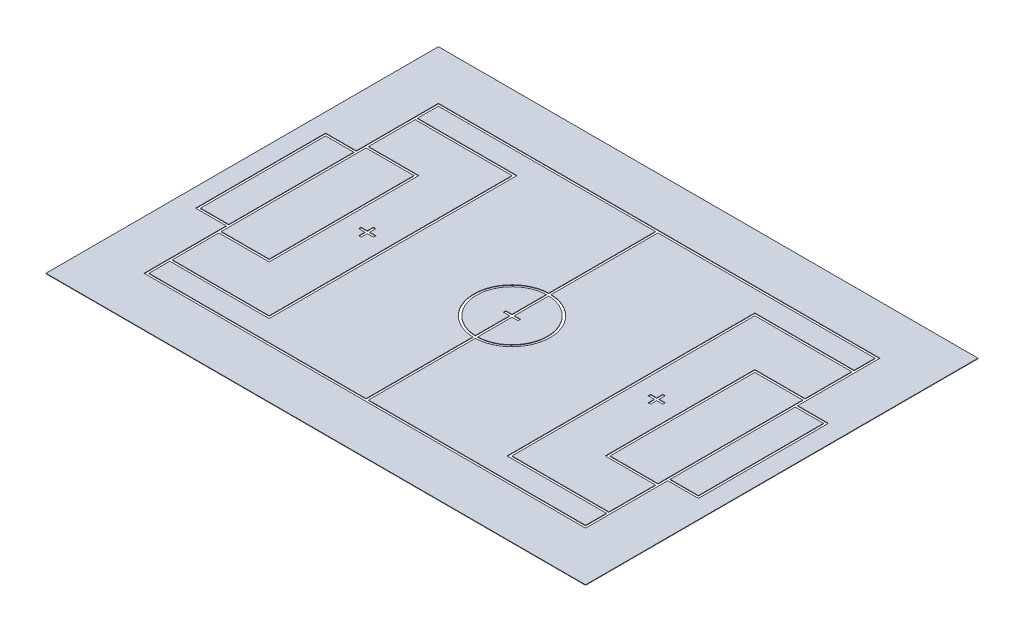
SolidWorks part; units mm, degrees
ref_plane "Front Plane" through (0, 0, 0) normal (0, 0, 1) x (1, 0, 0)
ref_plane "Top Plane" through (0, 0, 0) normal (0, 1, 0) x (1, 0, 0)
ref_plane "Right Plane" through (0, 0, 0) normal (1, 0, 0) x (0, 0, -1)
sketch "Sketch1" plane through (0, 0, 0) normal (0, 1, 0) x (1, 0, 0)
  line L0 (-4450, 2950) -> (-4450, 2525)
  line L1 (-5500, 4000) -> (5500, 4000)
  line L2 (-5500, 4000) -> (-5500, -4000)
  line L3 (-5500, -4000) -> (5500, -4000)
  line L4 (5500, 4000) -> (5500, -4000)
  line L5 (-4500, 3000) -> (4500, 3000)
  line L6 (-4500, 3000) -> (-4500, 1325)
  line L7 (-4500, -3000) -> (4500, -3000)
  line L8 (4500, 3000) -> (4500, 1325)
  line L9 (-4450, -2950) -> (-25, -2950)
  line L10 (4450, 2950) -> (4450, 2525)
  line L11 (-4450, 2950) -> (-25, 2950)
  line L12 (25, -2950) -> (4450, -2950)
  line L13 (-25, 2950) -> (-25, 773.6822)
  line L14 (25, 2950) -> (25, 773.6822)
  line L15 (-4450, -2950) -> (4450, -2950) construction
  line L16 (-25, 723.5912) -> (-25, 25)
  line L17 (25, 723.5912) -> (25, 25)
  line L18 (25, 2950) -> (4450, 2950)
  line L19 (-4450, 2950) -> (4450, 2950) construction
  line L20 (-25, -773.6822) -> (-25, -2950)
  line L21 (25, -773.6822) -> (25, -2950)
  line L22 (-150, 0) -> (150, 0) construction
  line L27 (-150, -25) -> (-25, -25)
  line L28 (-150, 25) -> (-25, 25)
  line L29 (-150, -25) -> (-150, 25)
  line L30 (150, -25) -> (150, 25)
  line L31 (25, 25) -> (150, 25)
  line L32 (-150, 25) -> (150, 25) construction
  line L33 (25, -25) -> (150, -25)
  line L34 (-150, -25) -> (150, -25) construction
  line L35 (-25, -25) -> (-25, -723.5912)
  line L36 (25, -25) -> (25, -723.5912)
  line L37 (-4450, 1500) -> (-3450, 1500) construction
  line L38 (-3450, 1500) -> (-3450, -1500) construction
  line L39 (-3450, -1500) -> (-4450, -1500) construction
  line L40 (-4450, 2500) -> (-2450, 2500) construction
  line L41 (-2450, 2500) -> (-2450, -2500) construction
  line L42 (-2450, -2500) -> (-4450, -2500) construction
  line L43 (-4450, 1475) -> (-3475, 1475)
  line L44 (-3475, 1475) -> (-3475, -1475)
  line L45 (-3475, -1475) -> (-4450, -1475)
  line L46 (-4450, 2475) -> (-2475, 2475)
  line L47 (-2475, 2475) -> (-2475, -2475)
  line L48 (-2475, -2475) -> (-4450, -2475)
  line L49 (-4450, 1525) -> (-3425, 1525)
  line L50 (-3425, 1525) -> (-3425, -1525)
  line L51 (-3425, -1525) -> (-4450, -1525)
  line L52 (-4450, 2525) -> (-2425, 2525)
  line L53 (-2425, 2525) -> (-2425, -2525)
  line L54 (-2425, -2525) -> (-4450, -2525)
  line L59 (-4450, 1475) -> (-4450, -1475)
  line L60 (-4450, 2950) -> (-4450, -2950) construction
  line L61 (-4450, 2475) -> (-4450, 1525)
  line L62 (-4450, -2525) -> (-4450, -2950)
  line L63 (-4450, -1525) -> (-4450, -2475)
  line L64 (-3100, 0) -> (-2800, 0) construction
  line L65 (-2950, 150) -> (-2950, -150) construction
  line L66 (-2975, 150) -> (-2975, 25)
  line L67 (-3100, -25) -> (-2975, -25)
  line L68 (-2925, 150) -> (-2925, 25)
  line L69 (-3100, 25) -> (-2975, 25)
  line L70 (-2975, 150) -> (-2925, 150)
  line L71 (-2975, -150) -> (-2925, -150)
  line L72 (-3100, -25) -> (-3100, 25)
  line L73 (-2800, -25) -> (-2800, 25)
  line L74 (-2975, -25) -> (-2975, -150)
  line L75 (-2975, 150) -> (-2975, -150) construction
  line L76 (-2925, 25) -> (-2800, 25)
  line L77 (-3100, 25) -> (-2800, 25) construction
  line L78 (-2925, -25) -> (-2925, -150)
  line L79 (-2925, 150) -> (-2925, -150) construction
  line L80 (-2925, -25) -> (-2800, -25)
  line L81 (-3100, -25) -> (-2800, -25) construction
  line L82 (-4500, 1300) -> (-5100, 1300) construction
  line L83 (-5100, 1300) -> (-5100, -1300) construction
  line L84 (-5100, -1300) -> (-4500, -1300) construction
  line L85 (-4500, 1325) -> (-5125, 1325)
  line L86 (-5125, 1325) -> (-5125, -1325)
  line L87 (-5125, -1325) -> (-4500, -1325)
  line L88 (-4500, 1275) -> (-5075, 1275)
  line L89 (-5075, 1275) -> (-5075, -1275)
  line L90 (-5075, -1275) -> (-4500, -1275)
  line L93 (-4500, -1325) -> (-4500, -3000)
  line L94 (-4500, 3000) -> (-4500, -3000) construction
  line L95 (-4500, 1275) -> (-4500, -1275)
  line L96 (0, 3000) -> (0, -3000) construction
  line L97 (5100, -1300) -> (4500, -1300) construction
  line L98 (5100, 1300) -> (5100, -1300) construction
  line L99 (4500, 1300) -> (5100, 1300) construction
  line L100 (2950, 150) -> (2950, -150) construction
  line L101 (3100, 0) -> (2800, 0) construction
  line L102 (2450, -2500) -> (4450, -2500) construction
  line L103 (2450, 2500) -> (2450, -2500) construction
  line L104 (4450, 2500) -> (2450, 2500) construction
  line L105 (3450, -1500) -> (4450, -1500) construction
  line L106 (3450, 1500) -> (3450, -1500) construction
  line L107 (4450, 1500) -> (3450, 1500) construction
  line L108 (4500, 1275) -> (4500, -1275)
  line L109 (5075, -1275) -> (4500, -1275)
  line L110 (5075, 1275) -> (5075, -1275)
  line L111 (4500, 1275) -> (5075, 1275)
  line L112 (5125, -1325) -> (4500, -1325)
  line L113 (5125, 1325) -> (5125, -1325)
  line L114 (4500, 1325) -> (5125, 1325)
  line L115 (2925, -25) -> (2800, -25)
  line L116 (2925, -25) -> (2925, -150)
  line L117 (2925, 25) -> (2800, 25)
  line L118 (2975, -25) -> (2975, -150)
  line L119 (2800, -25) -> (2800, 25)
  line L120 (3100, -25) -> (3100, 25)
  line L121 (2975, -150) -> (2925, -150)
  line L122 (2975, 150) -> (2925, 150)
  line L123 (3100, 25) -> (2975, 25)
  line L124 (2925, 150) -> (2925, 25)
  line L125 (3100, -25) -> (2975, -25)
  line L126 (2975, 150) -> (2975, 25)
  line L127 (2425, -2525) -> (4450, -2525)
  line L128 (2425, 2525) -> (2425, -2525)
  line L129 (4450, 2525) -> (2425, 2525)
  line L130 (3425, -1525) -> (4450, -1525)
  line L131 (3425, 1525) -> (3425, -1525)
  line L132 (4450, 1525) -> (3425, 1525)
  line L133 (2475, -2475) -> (4450, -2475)
  line L134 (2475, 2475) -> (2475, -2475)
  line L135 (4450, 2475) -> (2475, 2475)
  line L136 (3475, -1475) -> (4450, -1475)
  line L137 (3475, 1475) -> (3475, -1475)
  line L138 (4450, 1475) -> (3475, 1475)
  line L139 (4450, 2475) -> (4450, 1525)
  line L140 (4450, 2950) -> (4450, -2950) construction
  line L141 (4450, 1475) -> (4450, -1475)
  line L142 (4500, 1275) -> (4500, -1275)
  line L143 (4500, 3000) -> (4500, -3000) construction
  line L144 (4450, -1525) -> (4450, -2475)
  line L145 (4500, -1325) -> (4500, -3000)
  line L146 (4450, -2525) -> (4450, -2950)
  arc A1 (-25, 773.6822) -> (-25, -773.6822) centre (0, 0) ccw
  arc A2 (-25, 723.5912) -> (-25, -723.5912) centre (0, 0) ccw
  arc A3 (25, -773.6822) -> (25, 773.6822) centre (0, 0) ccw
  arc A6 (25, -723.5912) -> (25, 723.5912) centre (0, 0) ccw
  point P4 (0, 4000)
  point P6 (5500, 0)
  point P25 (0, 0)
  point P70 (-2950, 0)
  point P71 (-2950, 0)
  dimension "D8" = 300
  dimension "D1" = 11000
  dimension "D2" = 8000
  dimension "D3" = 1000
  dimension "D4" = 1000
  dimension "D5" = 1000
  dimension "D6" = 1000
  dimension "D11" = 3000
  dimension "D12" = 1000
  dimension "D13" = 5000
  dimension "D14" = 2000
  dimension "D17" = 300
  dimension "D18" = 300
  dimension "D19" = 1500
  dimension "D22" = 2600
  dimension "D23" = 600
  dimension "D26" = 25
  dimension "D27" = 50
  dimension "D7" = 50
  dimension "D9" = 25
  dimension "D10" = 25
  dimension "D15" = 25
  dimension "D16" = 25
  dimension "D20" = 25
  dimension "D21" = 25
  dimension "D24" = 25
  dimension "D25" = 25
extrude "Boss-Extrude1" add sketch "Sketch1" along normal blind 10 contours L36 A6 L17 L31 L30 L33 | L16 A2 L35 L27 L29 L28 | A1 L13 L11 L0 L52 L53 L54 L62 L9 L20 | A3 L21 L12 L146 L127 L128 L129 L10 L18 L14 | L144 L130 L131 L132 L139 L135 L134 L133 L122 L126 L123 L120 L125 L118 L121 L116 L115 L119 L117 L124 | L141 L138 L137 L136 | L111 L108 L109 L110 | L51 L63 L48 L47 L46 L61 L49 L50 L80 L78 L71 L74 L67 L72 L69 L66 L70 L68 L76 L73 | L43 L59 L45 L44 | L95 L88 L89 L90 | L4 L1 L2 L3 L112 L145 L7 L93 L87 L86 L85 L6 L5 L8 L114 L113
